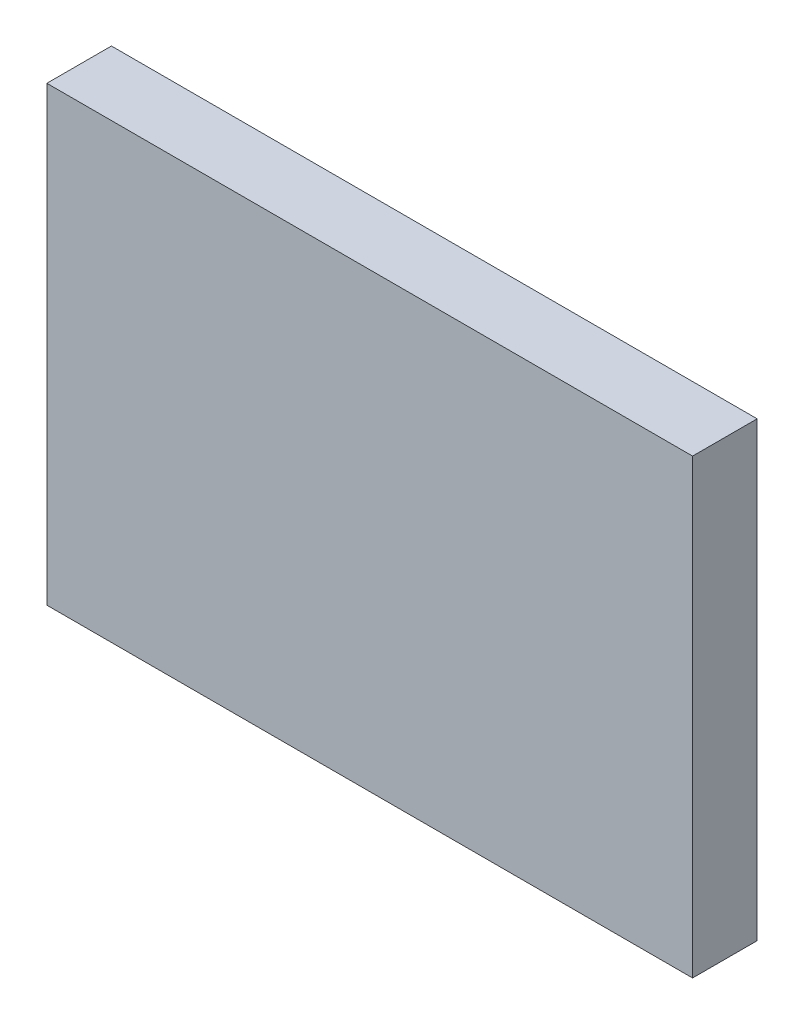
SolidWorks part; units mm, degrees
ref_plane "Front Plane" through (0, 0, 0) normal (0, 0, 1) x (1, 0, 0)
ref_plane "Top Plane" through (0, 0, 0) normal (0, 1, 0) x (1, 0, 0)
ref_plane "Right Plane" through (0, 0, 0) normal (1, 0, 0) x (0, 0, -1)
sketch "Sketch1" plane through (0, 0, 0) normal (0, 0, 1) x (1, 0, 0)
  line L1 (0, 0) -> (100, 0)
  line L2 (0, 0) -> (0, 70)
  line L3 (0, 70) -> (100, 70)
  line L4 (100, 0) -> (100, 70)
  dimension "D1" = 70
  dimension "D2" = 100
extrude "Boss-Extrude1" add sketch "Sketch1" along normal blind 10 contours L2 L3 L4 L1
